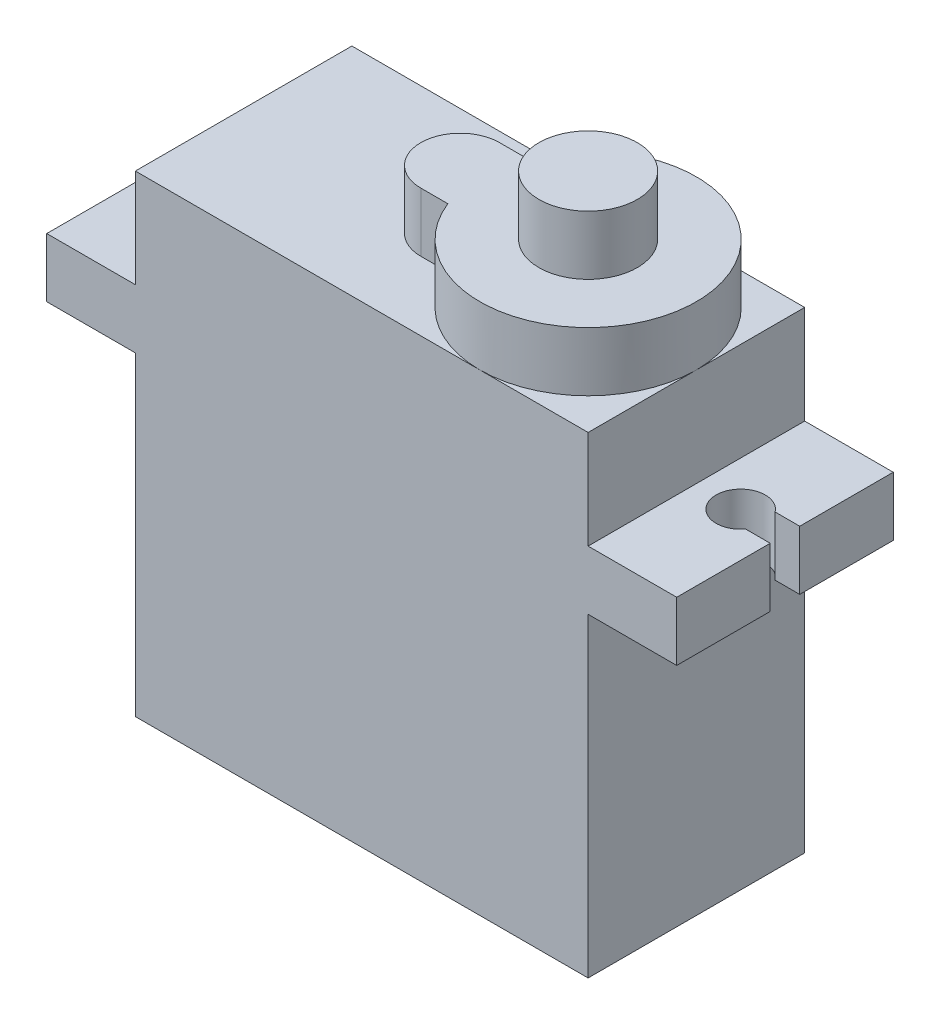
SolidWorks part; units mm, degrees
material "1060 Alloy"
ref_plane "Front Plane" through (0, 0, 0) normal (0, 0, 1) x (1, 0, 0)
ref_plane "Top Plane" through (0, 0, 0) normal (0, 1, 0) x (1, 0, 0)
ref_plane "Right Plane" through (0, 0, 0) normal (1, 0, 0) x (0, 0, -1)
sketch "Sketch1" plane through (0, 0, 0) normal (0, 1, 0) x (1, 0, 0)
  line L1 (-11.5, -5.5) -> (11.5, -5.5)
  line L2 (-11.5, -5.5) -> (-11.5, 5.5)
  line L3 (-11.5, 5.5) -> (11.5, 5.5)
  line L4 (11.5, -5.5) -> (11.5, 5.5)
  line L5 (-11.5, -5.5) -> (11.5, 5.5) construction
  line L6 (-11.5, 5.5) -> (11.5, -5.5) construction
  point P0 (0, 0)
  dimension "D1" = 11
  dimension "D2" = 23
extrude "Boss-Extrude1" add sketch "Sketch1" along normal blind 24
sketch "Sketch2" plane through (11.5, 0, 0) normal (1, 0, 0) x (0, 0, -1)
  line L0 (-5.5, 24) -> (-5.5, 0) construction
  line L1 (-5.5, 19) -> (5.5, 19)
  line L2 (-5.5, 19) -> (-5.5, 16)
  line L3 (-5.5, 16) -> (5.5, 16)
  line L4 (5.5, 19) -> (5.5, 16)
  line L5 (5.5, 24) -> (5.5, 0) construction
  line L7 (-5.5, 0) -> (5.5, 0) construction
  dimension "D1" = 16
  dimension "D2" = 3
extrude "Boss-Extrude2" add sketch "Sketch2" along normal blind 4.5 and the other way blind 27.5
sketch "Sketch3" plane through (0, 24, 0) normal (0, 1, 0) x (1, 0, 0)
  line L0 (11.5, -5.5) -> (11.5, 5.5) construction
  line L3 (-0.5, 2) -> (0.8765, 2)
  line L4 (-0.5, -2) -> (0.8765, -2)
  line L5 (-11.5, 5.5) -> (-11.5, -5.5) construction
  line L6 (11.5, -5.5) -> (11.5, 5.5) construction
  circle A0 centre (6, 0) radius 2.5
  arc A1 (0.8765, -2) -> (0.8765, 2) centre (6, 0) ccw
  arc A2 (-0.5, 2) -> (-0.5, -2) centre (-0.5, 0) ccw
  dimension "D1" = 5
  dimension "D3" = 2
  dimension "D2" = 11
  dimension "D4" = 5.5
extrude "Boss-Extrude3" add sketch "Sketch3" along normal blind 3
sketch "Sketch4" plane through (0, 27, 0) normal (0, 1, 0) x (1, 0, 0)
  circle A0 centre (6, 0) radius 2.5
extrude "Boss-Extrude4" add sketch "Sketch4" along normal blind 3 and the other way up to surface (27 mm away)
sketch "Sketch5" plane through (0, 19, 0) normal (0, 1, 0) x (1, 0, 0)
  line L0 (-16, -0.75) -> (-14.75, -0.75)
  line L1 (-16, 5.5) -> (-16, -5.5) construction
  line L3 (-14.75, 0.75) -> (-16, 0.75)
  line L4 (-16, 0.75) -> (-16, -0.75)
  line L5 (14.75, 0.75) -> (16, 0.75)
  line L6 (16, 5.5) -> (16, -5.5) construction
  line L7 (16, 0.75) -> (16, -0.75)
  line L8 (16, -0.75) -> (14.75, -0.75)
  arc A0 (-14.75, -0.75) -> (-14.75, 0.75) centre (-13.75, 0) ccw
  arc A1 (14.75, 0.75) -> (14.75, -0.75) centre (13.75, 0) ccw
  point P1 (-16, 0)
  dimension "D1" = 2.5
  dimension "D2" = 1.5
  dimension "D3" = 27.5
extrude "Cut-Extrude1" cut sketch "Sketch5" against normal blind 4
equation "\"D2@Sketch3\"=9+\"D3@Sketch3\""
